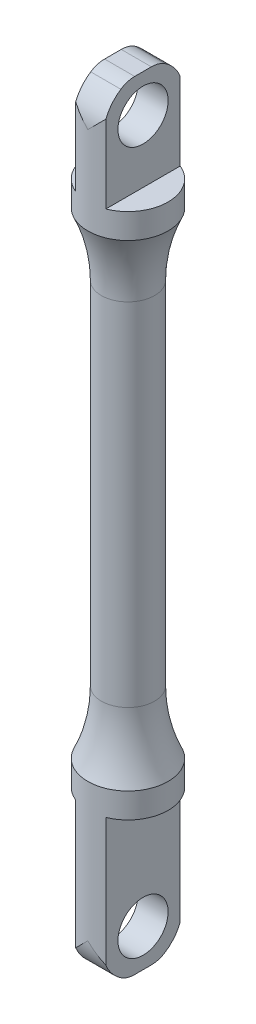
SolidWorks part; units mm, degrees
material "Chrome Stainless Steel"
ref_plane "Front Plane" through (0, 0, 0) normal (0, 0, 1) x (1, 0, 0)
ref_plane "Top Plane" through (0, 0, 0) normal (0, 1, 0) x (1, 0, 0)
ref_plane "Right Plane" through (0, 0, 0) normal (1, 0, 0) x (0, 0, -1)
sketch "Sketch1" plane through (0, 0, 0) normal (0, 0, 1) x (1, 0, 0)
  line L0 (0, 0) -> (0, -52.5)
  line L1 (8, -52.5) -> (8, -47.5)
  line L2 (0, -52.5) -> (8, -52.5)
  line L3 (5.3, 0) -> (5.3, -35)
  line L5 (5.3, 0) -> (0, 0)
  arc A0 (5.3, -35) -> (8, -47.5) centre (35.5852, -35) ccw
  dimension "D1" = 5
  dimension "D2" = 52.5
  dimension "D3" = 35
  dimension "D4" = 8
  dimension "D5" = 5.3
revolve "Revolve1" add sketch "Sketch1" angle 360 about L0
mirror "Mirror1" about plane through (5.3, 0, 0) normal (0, -1, 0) of "Revolve1"
sketch "Sketch3" plane through (0, 52.5, 0) normal (0, 1, 0) x (1, 0, 0)
  line L0 (-3, 7.4162) -> (-3, -7.4162)
  line L1 (3, 7.4162) -> (3, -7.4162)
  circle A0 centre (0, 0) radius 8 construction
  arc A1 (-3, -7.4162) -> (3, -7.4162) centre (0, 0) ccw
  arc A2 (3, 7.4162) -> (-3, 7.4162) centre (0, 0) ccw
  dimension "D1" = 6
extrude "Boss-Extrude1" add sketch "Sketch3" along normal blind 20
sketch "Sketch4" plane through (0, -52.5, 0) normal (0, -1, 0) x (1, 0, 0)
  line L0 (3, 7.4162) -> (3, -7.4162)
  line L1 (-3, 7.4162) -> (-3, -7.4162)
  arc A0 (3, -7.4162) -> (-3, -7.4162) centre (0, 0) cw
  arc A1 (-3, 7.4162) -> (3, 7.4162) centre (0, 0) cw
  circle A2 centre (0, 0) radius 8 construction
  dimension "D1" = 6
extrude "Boss-Extrude2" add sketch "Sketch4" along normal blind 30
sketch "Sketch5" plane through (-3, 0, 0) normal (-1, 0, 0) x (0, 0, 1)
  line L0 (-7.4162, 72.5) -> (7.4162, 72.5) construction
  line L1 (7.4162, -82.5) -> (-7.4162, -82.5) construction
  line L2 (8, 47.5) -> (8, 72.5) construction
  line L3 (-18.4072, 86.2255) -> (21.7133, 86.2255)
  line L4 (-18.4072, 86.2255) -> (-18.4072, 65)
  line L5 (-18.4072, 65) -> (-8, 65)
  line L6 (21.7133, 86.2255) -> (21.7133, 65)
  line L7 (8, 65) -> (21.7133, 65)
  line L8 (8, -82.5) -> (8, -47.5) construction
  line L9 (21.7133, -75) -> (8, -75)
  line L10 (21.7133, -75) -> (21.7133, -89.5427)
  line L11 (21.7133, -89.5427) -> (-18.4072, -89.5427)
  line L12 (-18.4072, -75) -> (-18.4072, -89.5427)
  line L13 (-8, -75) -> (-18.4072, -75)
  circle A0 centre (0, 65) radius 5
  circle A1 centre (0, -75) radius 5
  arc A2 (8, 65) -> (-8, 65) centre (0, 65) ccw
  arc A3 (8, -75) -> (-8, -75) centre (0, -75) cw
  dimension "D1" = 10
  dimension "D2" = 140
  dimension "D3" = 7.5
  dimension "D4" = 7.5
extrude "Cut-Extrude1" cut sketch "Sketch5" against normal through all both and the other way through all
fillet "Fillet6" radius 5 4 edges at (0, 72.5, -2.7839) (0, 72.5, 2.7839) (0, -82.5, -2.7839) (0, -82.5, 2.7839)
